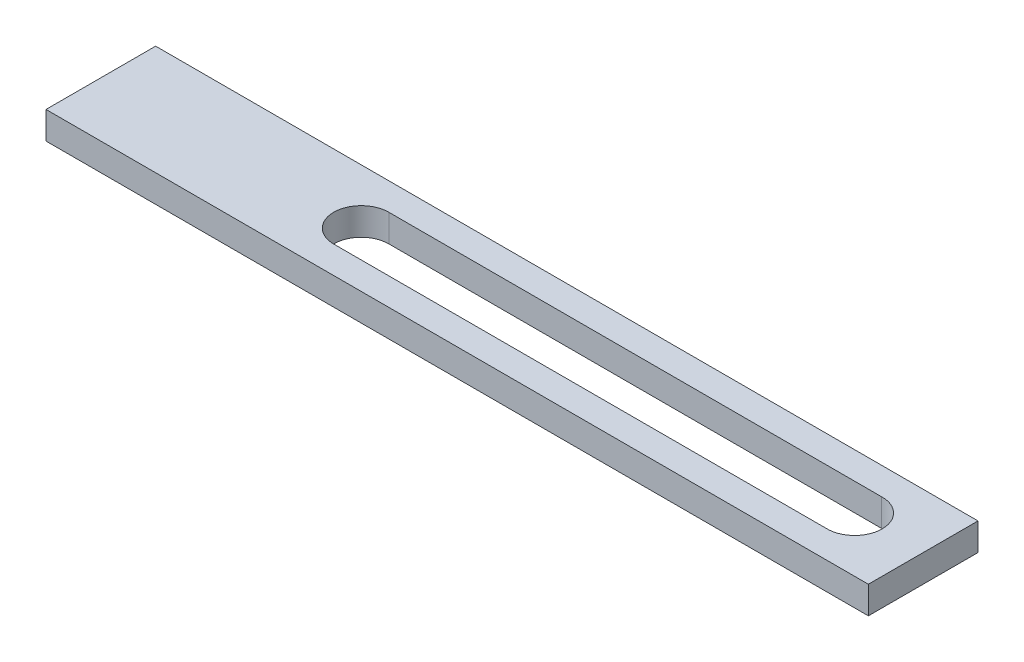
SolidWorks part; units mm, degrees
material "Простая углеродистая сталь"
ref_plane "Спереди" through (0, 0, 0) normal (0, 0, 1) x (1, 0, 0)
ref_plane "Сверху" through (0, 0, 0) normal (0, 1, 0) x (1, 0, 0)
ref_plane "Справа" through (0, 0, 0) normal (1, 0, 0) x (0, 0, -1)
sketch "Эскиз1" plane through (0, 0, 0) normal (0, 1, 0) x (1, 0, 0)
  line L1 (0, 0) -> (300, 0)
  line L2 (0, 0) -> (0, 40)
  line L3 (0, 40) -> (300, 40)
  line L4 (300, 0) -> (300, 40)
extrude "Бобышка-Вытянуть1" add sketch "Эскиз1" along normal blind 10
sketch "Эскиз2" plane through (0, 10, 0) normal (0, 1, 0) x (1, 0, 0)
  line L0 (95, 9.95) -> (274.7214, 9.9539)
  line L1 (95, 30.05) -> (274.7214, 30.0461)
  arc A0 (95, 30.05) -> (95, 9.95) centre (95, 20) ccw
  arc A1 (274.7214, 30.0461) -> (274.7214, 9.9539) centre (275, 20) cw
extrude "Вырез-Вытянуть1" cut sketch "Эскиз2" against normal up to next
